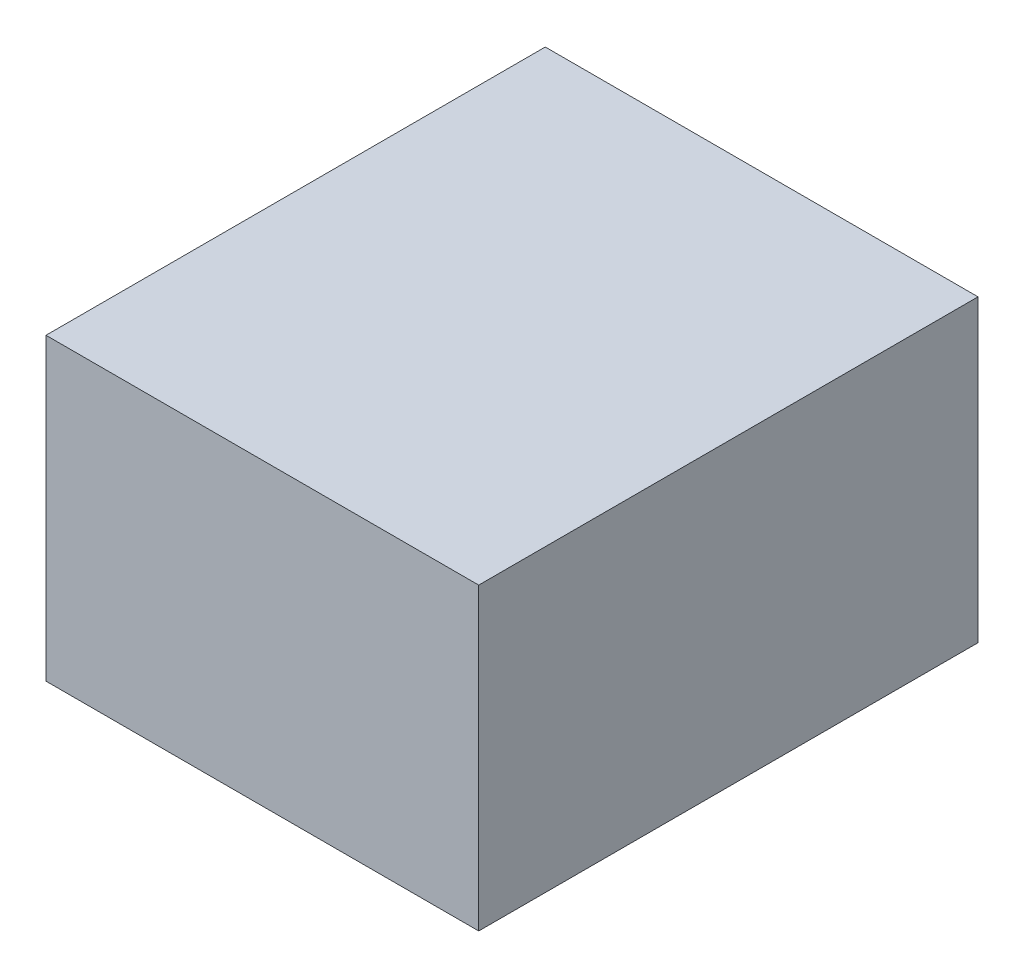
SolidWorks part; units mm, degrees
ref_plane "Front Plane" through (0, 0, 0) normal (0, 0, 1) x (1, 0, 0)
ref_plane "Top Plane" through (0, 0, 0) normal (0, 1, 0) x (1, 0, 0)
ref_plane "Right Plane" through (0, 0, 0) normal (1, 0, 0) x (0, 0, -1)
sketch "Sketch1" plane through (0, 0, 0) normal (0, 0, 1) x (1, 0, 0)
  line L1 (0, 0) -> (330.2, 0)
  line L2 (0, 0) -> (0, 228.6)
  line L3 (0, 228.6) -> (330.2, 228.6)
  line L4 (330.2, 0) -> (330.2, 228.6)
  dimension "D1" = 330.2
  dimension "D2" = 228.6
extrude "Boss-Extrude1" add sketch "Sketch1" along normal blind 381
